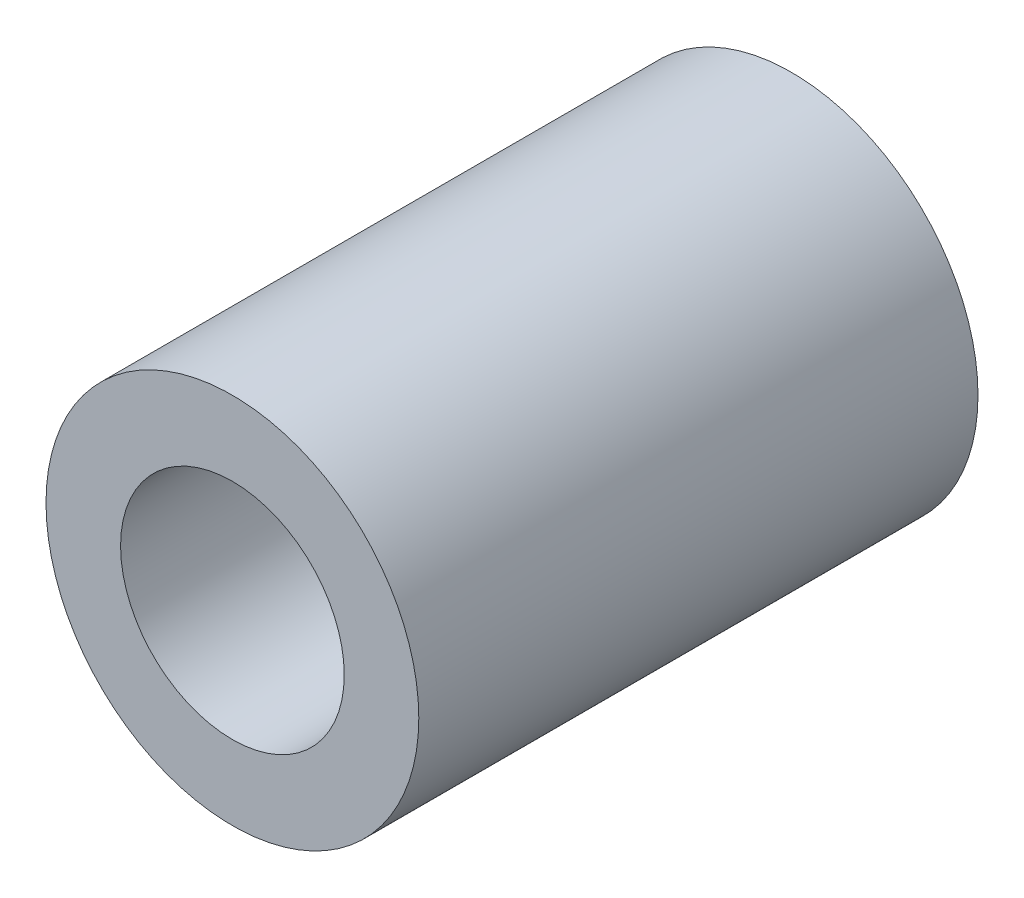
SolidWorks part; units mm, degrees
material "ﾎﾟﾘｵｷｼﾒﾁﾚﾝ(POM)ｱｾﾀｰﾙ共重合体"
ref_plane "Front Plane" through (0, 0, 0) normal (0, 0, 1) x (1, 0, 0)
ref_plane "Top Plane" through (0, 0, 0) normal (0, 1, 0) x (1, 0, 0)
ref_plane "Right Plane" through (0, 0, 0) normal (1, 0, 0) x (0, 0, -1)
sketch "Sketch2" plane through (0, 0, 0) normal (0, 0, 1) x (1, 0, 0)
  circle A0 centre (0, 0) radius 2.5
  circle A1 centre (0, 0) radius 1.5
  dimension "D1" = 3
  dimension "D2" = 5
  dimension "D3" = 5
extrude "Boss-Extrude1" add sketch "Sketch2" along normal blind 7.5
